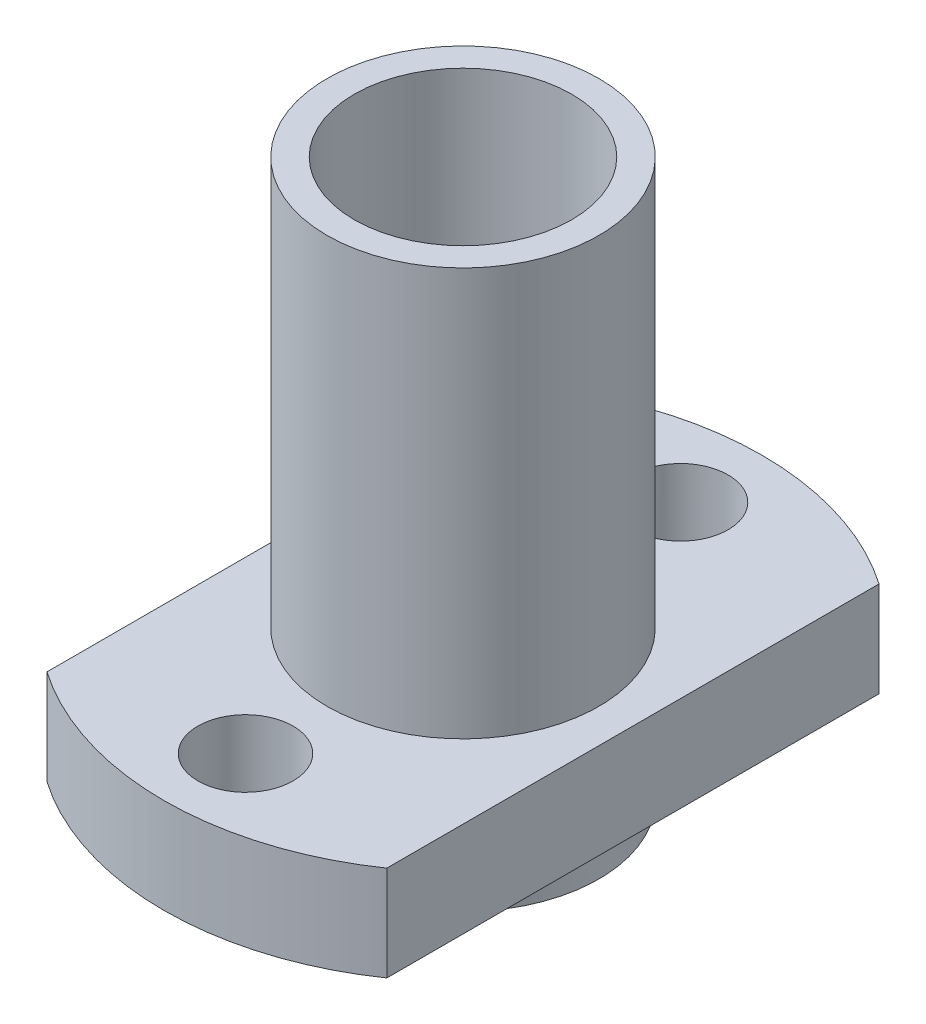
SolidWorks part; units mm, degrees
ref_plane "前视基准面" through (0, 0, 0) normal (0, 0, 1) x (1, 0, 0)
ref_plane "上视基准面" through (0, 0, 0) normal (0, 1, 0) x (1, 0, 0)
ref_plane "右视基准面" through (0, 0, 0) normal (1, 0, 0) x (0, 0, -1)
ref_plane "基准面4" through (0, 1.5, 0) normal (0, -1, 0) x (1, 0, 0)
sketch "草图1" plane through (0, 1.5, 0) normal (0, -1, 0) x (1, 0, 0)
  circle A1 centre (0, 0) radius 11
  dimension "D1" = 22
extrude "凸台-拉伸1" add sketch "草图1" against normal blind 3.5
sketch "草图2" plane through (0, 5, 0) normal (0, 1, 0) x (1, 0, 0)
  circle A0 centre (0, 0) radius 5
  circle A1 centre (0, 0) radius 4
  dimension "D1" = 10
  dimension "D2" = 8
extrude "凸台-拉伸2" add sketch "草图2" along normal blind 15 and the other way blind 5.5
sketch "草图3" plane through (0, 5, 0) normal (0, 1, 0) x (1, 0, 0)
  circle A0 centre (0, 0) radius 8 construction
  circle A1 centre (0, 0) radius 4
  circle A2 centre (0, 0) radius 4
  circle A3 centre (-8, 0) radius 1.75
  circle A4 centre (0, 8) radius 1.75
  circle A5 centre (8, 0) radius 1.75
  circle A6 centre (0, -8) radius 1.75
  point P15 (0, 0)
  dimension "D2" = 16
  dimension "D3" = 3.5
  dimension "D5" = 90
  dimension "D1" = 0
  dimension "D4" = 4
extrude "切除-拉伸1" cut sketch "草图3" against normal through all
sketch "草图4" plane through (0, 1.5, 0) normal (0, -1, 0) x (1, 0, 0)
  line L0 (-6.25, -9.0519) -> (-6.25, 9.0519)
  line L1 (6.25, 9.0519) -> (6.25, -9.0519)
  circle A0 centre (0, 0) radius 11 construction
  arc A1 (-6.25, 9.0519) -> (-6.25, -9.0519) centre (0, 0) ccw
  circle A2 centre (8, 0) radius 1.75 construction
  circle A3 centre (-8, 0) radius 1.75 construction
  arc A4 (6.25, -9.0519) -> (6.25, 9.0519) centre (0, 0) ccw
extrude "切除-拉伸2" cut sketch "草图4" against normal blind 10
